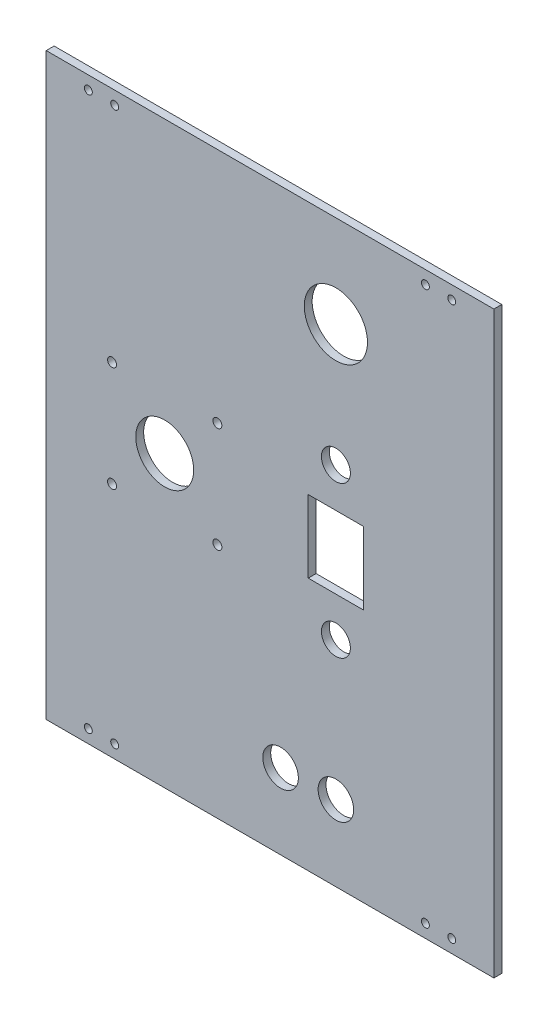
SolidWorks part; units mm, degrees
ref_plane "Plan de face" through (0, 0, 0) normal (0, 0, 1) x (1, 0, 0)
ref_plane "Plan de dessus" through (0, 0, 0) normal (0, 1, 0) x (1, 0, 0)
ref_plane "Plan de droite" through (0, 0, 0) normal (1, 0, 0) x (0, 0, -1)
sketch "Esquisse1" plane through (0, 0, 0) normal (0, 0, 1) x (1, 0, 0)
  line L1 (99.8748, 40.2199) -> (-70.1252, 40.2199)
  line L2 (99.8748, 40.2199) -> (99.8748, -179.7801)
  line L3 (99.8748, -179.7801) -> (-70.1252, -179.7801)
  line L4 (-70.1252, 40.2199) -> (-70.1252, -179.7801)
  line L5 (-70.1252, -69.7801) -> (99.8748, -69.7801) construction
  line L6 (14.8748, 40.2199) -> (14.8748, -179.7801) construction
  line L8 (50.3748, -56.0301) -> (29.3748, -56.0301)
  line L9 (50.3748, -56.0301) -> (50.3748, -83.5301)
  line L10 (50.3748, -83.5301) -> (29.3748, -83.5301)
  line L11 (29.3748, -56.0301) -> (29.3748, -83.5301)
  circle A0 centre (-25.1252, -69.7801) radius 11
  circle A1 centre (-5.1252, -89.7801) radius 1.7
  circle A2 centre (-45.1252, -89.7801) radius 1.7
  circle A3 centre (-45.1252, -49.7801) radius 1.7
  circle A4 centre (-5.1252, -49.7801) radius 1.7
  circle A5 centre (83.8748, -174.7801) radius 1.5
  circle A6 centre (73.8748, -174.7801) radius 1.5
  circle A7 centre (83.8748, 35.2199) radius 1.5
  circle A8 centre (73.8748, 35.2199) radius 1.5
  circle A9 centre (-44.1252, -174.7801) radius 1.5
  circle A10 centre (-54.1252, -174.7801) radius 1.5
  circle A11 centre (-44.1252, 35.2199) radius 1.5
  circle A12 centre (-54.1252, 35.2199) radius 1.5
  circle A13 centre (39.8748, 5.2199) radius 12
  circle A14 centre (39.8748, -41.0301) radius 5.5
  circle A15 centre (39.8748, -98.5301) radius 5.5
  circle A16 centre (39.8748, -151.105) radius 6.75
  circle A17 centre (18.8748, -151.105) radius 6.75
  point P5 (39.8748, -83.5301)
  point P10 (14.8748, 40.2199)
  dimension "D3" = 20
  dimension "D4" = 20
  dimension "D8" = 3
  dimension "D11" = 24
  dimension "D15" = 11
  dimension "D17" = 35
  dimension "D18" = 3.4
  dimension "D19" = 13.5
  dimension "D25" = 22
  dimension "D1" = 220
  dimension "D2" = 170
  dimension "D10" = 5
  dimension "D13" = 27.5
  dimension "D14" = 21
  dimension "D6" = 40
  dimension "D7" = 4
  dimension "D16" = 15
  dimension "D20" = 10
  dimension "D21" = 16
  dimension "D22" = 60
  dimension "D23" = 21
  dimension "D24" = 20
extrude "Boss.-Extru.1" add sketch "Esquisse1" along normal blind 3
